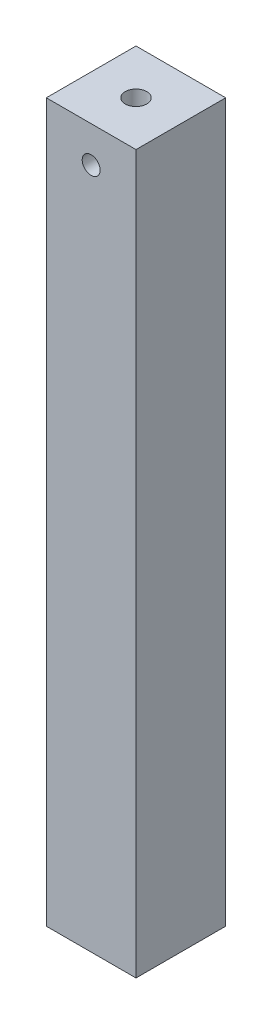
SolidWorks part; units mm, degrees
ref_plane "Front Plane" through (0, 0, 0) normal (0, 0, 1) x (1, 0, 0)
ref_plane "Top Plane" through (0, 0, 0) normal (0, 1, 0) x (1, 0, 0)
ref_plane "Right Plane" through (0, 0, 0) normal (1, 0, 0) x (0, 0, -1)
sketch "Sketch1" plane through (0, 0, 0) normal (0, 1, 0) x (1, 0, 0)
  line L1 (5.0862, -14.8276) -> (-19.9138, -14.8276)
  line L2 (5.0862, -14.8276) -> (5.0862, 10.1724)
  line L3 (5.0862, 10.1724) -> (-19.9138, 10.1724)
  line L4 (-19.9138, -14.8276) -> (-19.9138, 10.1724)
  circle A0 centre (-7.4138, -2.3276) radius 3
  dimension "D3" = 6
  dimension "D4" = 12.5
  dimension "D5" = 12.5
  dimension "D1" = 25
  dimension "D2" = 25
extrude "Boss-Extrude1" add sketch "Sketch1" along normal blind 200
sketch "Sketch2" plane through (0, 0, 14.8276) normal (0, 0, 1) x (1, 0, 0)
  line L0 (-19.9138, 200) -> (-19.9138, 0) construction
  line L1 (-19.9138, 200) -> (5.0862, 200) construction
  circle A0 centre (-7.4138, 190) radius 2.5
  dimension "D1" = 5
  dimension "D2" = 12.5
  dimension "D3" = 10
extrude "Cut-Extrude1" cut sketch "Sketch2" against normal through all
sketch "Sketch3" plane through (0, 200, 0) normal (0, 1, 0) x (1, 0, 0)
  line L0 (5.0862, -14.8276) -> (5.0862, 10.1724) construction
  line L1 (-19.9138, -14.8276) -> (5.0862, -14.8276) construction
  circle A0 centre (-4.9138, -4.8276) radius 3
  dimension "D1" = 6
  dimension "D2" = 10
  dimension "D3" = 10
